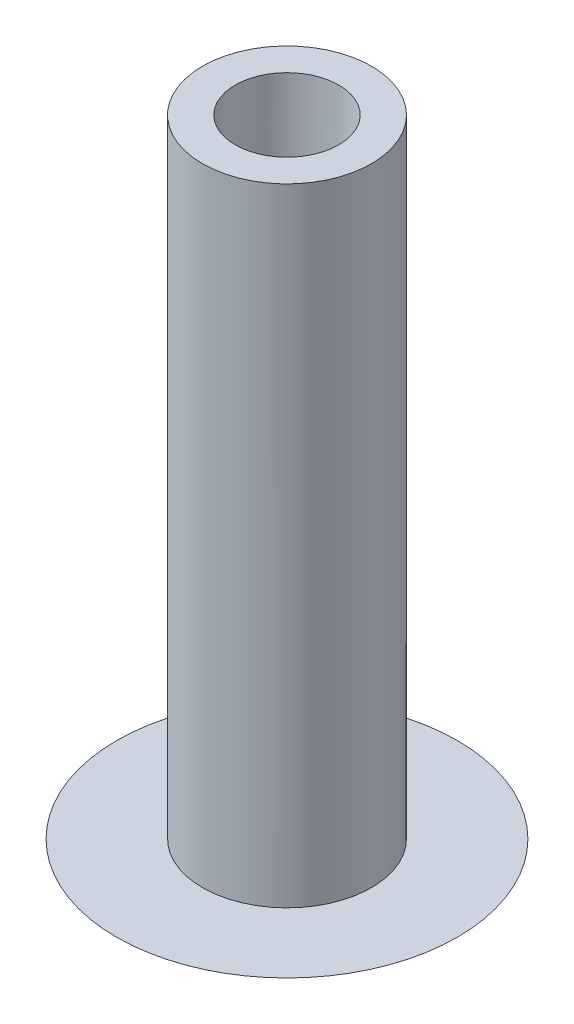
SolidWorks part; units mm, degrees
ref_plane "Front Plane" through (0, 0, 0) normal (0, 0, 1) x (1, 0, 0)
ref_plane "Top Plane" through (0, 0, 0) normal (0, 1, 0) x (1, 0, 0)
ref_plane "Right Plane" through (0, 0, 0) normal (1, 0, 0) x (0, 0, -1)
sketch "Sketch1" plane through (0, 0, 0) normal (0, 1, 0) x (1, 0, 0)
  circle A0 centre (0, 0) radius 3.937
  circle A1 centre (0, 0) radius 2.413
  dimension "D1" = 7.874
  dimension "D2" = 4.826
extrude "Boss-Extrude1" add sketch "Sketch1" along normal blind 29.21
sketch "Sketch2" plane through (0, 0, 0) normal (0, 0, 1) x (1, 0, 0)
  line L0 (-7.9375, 0) -> (7.9375, 0)
  line L1 (0, 0) -> (0, -2.54)
  arc A0 (7.9375, 0) -> (-7.9375, 0) centre (0, 11.1323) cw
  point P4 (0, 0)
  dimension "D1" = 15.875
  dimension "D2" = 2.54
revolve "Revolve1" add sketch "Sketch2" angle 360 about L1
sketch "Sketch3" plane through (0, 0, 0) normal (0, 0, 1) x (1, 0, 0)
  line L0 (-2.413, 0) -> (-2.413, 29.21)
  line L1 (2.413, 29.21) -> (2.413, 0)
  line L2 (2.413, 29.21) -> (2.413, 0)
  line L3 (-2.413, 0) -> (-2.413, 29.21)
  line L4 (2.413, 29.21) -> (1.5367, 0)
  line L5 (3.937, 0) -> (-3.937, 0) construction
  line L6 (0, 0) -> (0, 29.628) construction
  line L10 (2.413, 0) -> (1.5367, 0)
  line L11 (2.413, 16.51) -> (-2.413, 16.51)
  line L12 (2.413, 16.51) -> (-2.413, 16.51)
  point P10 (2.032, 16.51)
  point P11 (0, 16.51)
  dimension "D2" = 2.032
  dimension "D1" = 12.7
revolve "Revolve2" add sketch "Sketch3" angle 360 about L6
